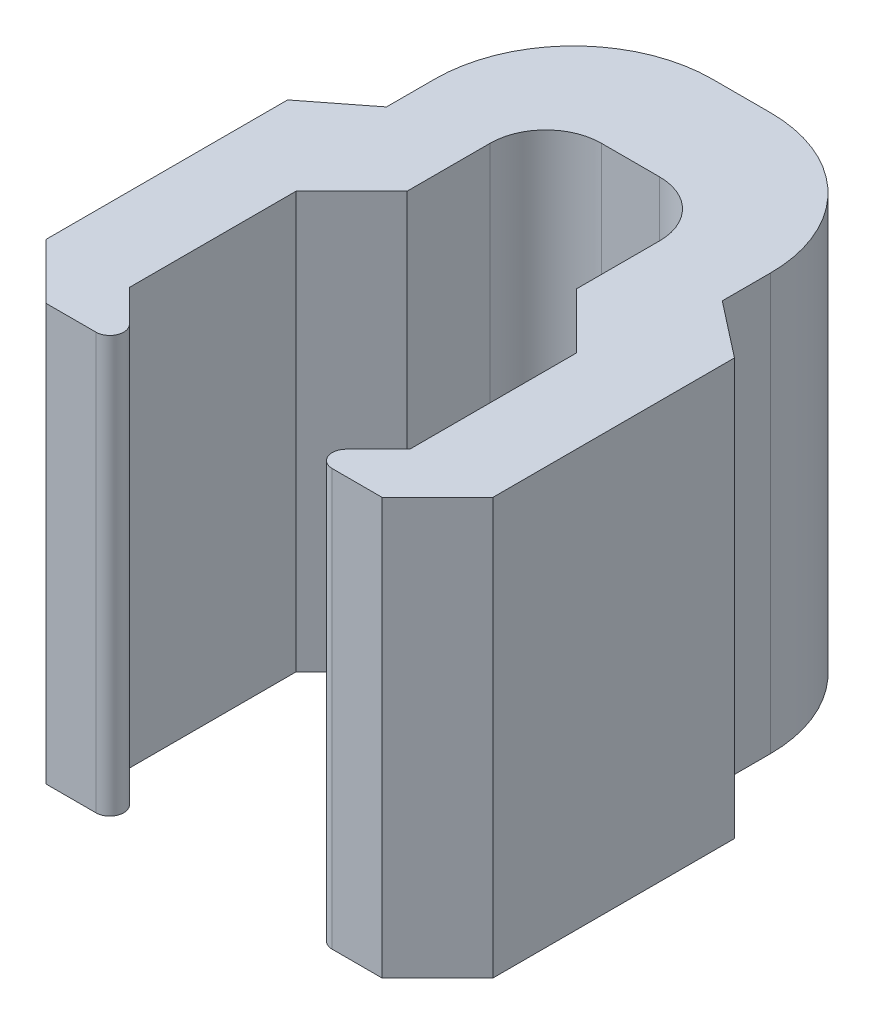
SolidWorks part; units mm, degrees
ref_plane "Front Plane" through (0, 0, 0) normal (0, 0, 1) x (1, 0, 0)
ref_plane "Top Plane" through (0, 0, 0) normal (0, 1, 0) x (1, 0, 0)
ref_plane "Right Plane" through (0, 0, 0) normal (1, 0, 0) x (0, 0, -1)
sketch "Sketch2" plane through (0, 0, 0) normal (0, 1, 0) x (1, 0, 0)
  line L0 (-11.1661, -0.629) -> (-14.1661, -0.629)
  line L1 (-11.1661, 14.371) -> (-1.0661, 14.371)
  line L2 (-11.1661, 14.371) -> (-11.1661, -0.629)
  line L3 (-11.1661, -0.629) -> (-1.0661, -0.629)
  line L4 (-1.0661, 14.371) -> (-1.0661, -0.629)
  line L5 (-14.1661, -0.629) -> (-14.1661, 18.371)
  line L6 (-14.1661, 18.371) -> (1.9339, 18.371)
  line L7 (1.9339, 18.371) -> (1.9339, -0.629)
  line L8 (1.9339, -0.629) -> (-1.0661, -0.629)
  line L9 (-11.1661, 1.371) -> (-9.1661, -0.629)
  line L10 (-1.0661, 1.371) -> (-3.0661, -0.629)
  line L11 (-11.1661, 7.371) -> (-9.1661, 9.371)
  line L12 (-9.1661, 9.371) -> (-9.1661, 14.371)
  line L13 (-3.0661, 9.371) -> (-1.0661, 7.371)
  line L14 (-3.0661, 9.371) -> (-3.0661, 14.371)
  line L15 (-14.1661, 10.071) -> (-12.1661, 11.6314)
  line L16 (-12.1661, 11.6314) -> (-12.1661, 18.371)
  line L17 (1.9339, 10.071) -> (-0.0661, 11.6314)
  line L18 (-0.0661, 11.6314) -> (-0.0661, 18.371)
  point P9 (-14.1661, 8.871)
  dimension "D1" = 10.1
  dimension "D2" = 15
  dimension "D3" = 3
  dimension "D4" = 3
  dimension "D5" = 4
  dimension "D6" = 2
  dimension "D7" = 2
  dimension "D8" = 10
  dimension "D9" = 3
extrude "Boss-Extrude1" add sketch "Sketch2" along normal blind 15 contours L8 L7 L6 L5 L0 L2 L1 L4 | L11 L12 L1 L2 | L14 L13 L4 L1 | L4 L10 L3 | L9 L2 L3
chamfer "Chamfer1" distance 2 angle 45 2 edges at (-14.1661, 7.5, 0.629) (1.9339, 7.5, 0.629)
fillet "Fillet1" radius 2 2 edges at (-3.0661, 7.5, -14.371) (-9.1661, 7.5, -14.371)
fillet "Fillet3" radius 5 2 edges at (-0.0661, 7.5, -18.371) (-12.1661, 7.5, -18.371)
fillet "Fillet4" radius 0.5 2 edges at (-3.0661, 7.5, 0.629) (-9.1661, 7.5, 0.629)
